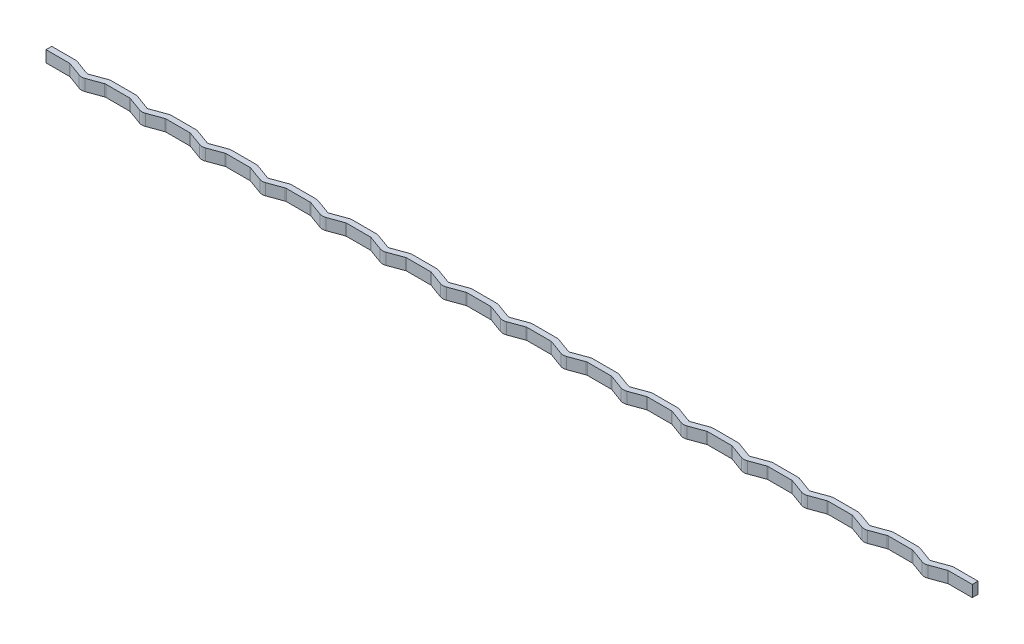
SolidWorks part; units mm, degrees
material "Rubber"
ref_plane "Front Plane" through (0, 0, 0) normal (0, 0, 1) x (1, 0, 0)
ref_plane "Top Plane" through (0, 0, 0) normal (0, 1, 0) x (1, 0, 0)
ref_plane "Right Plane" through (0, 0, 0) normal (1, 0, 0) x (0, 0, -1)
sketch "Sketch1" plane through (0, 0, 0) normal (0, 1, 0) x (1, 0, 0)
  line L0 (0, 0) -> (4.0737, 0)
  line L1 (4.25, 0) -> (10.25, 0) construction
  line L2 (7.25, 0.5445) -> (7.25, -3.0811) construction
  line L3 (10.4263, 0) -> (10.75, 0)
  line L4 (4.4157, -0.0603) -> (6.908, -0.9674)
  line L5 (7.592, -0.9674) -> (10.0843, -0.0603)
  line L6 (0, -0.5) -> (4.0737, -0.5)
  line L7 (4.2447, -0.5302) -> (6.737, -1.4373)
  line L8 (7.763, -1.4373) -> (10.2553, -0.5302)
  line L9 (10.4263, -0.5) -> (10.75, -0.5)
  line L10 (0, 0.5) -> (4.0737, 0.5)
  line L11 (4.5867, 0.4095) -> (7.079, -0.4976)
  line L12 (7.421, -0.4976) -> (9.9133, 0.4095)
  line L13 (10.4263, 0.5) -> (10.75, 0.5)
  line L14 (0, 0.5) -> (0, -0.5)
  line L15 (10.75, 0.5) -> (10.75, -0.5)
  arc A0 (4.4157, -0.0603) -> (4.0737, 0) centre (4.0737, -1) ccw
  arc A1 (10.4263, 0) -> (10.0843, -0.0603) centre (10.4263, -1) ccw
  arc A2 (7.592, -0.9674) -> (6.908, -0.9674) centre (7.25, -0.0277) cw
  arc A3 (4.2447, -0.5302) -> (4.0737, -0.5) centre (4.0737, -1) ccw
  arc A4 (7.763, -1.4373) -> (6.737, -1.4373) centre (7.25, -0.0277) cw
  arc A5 (10.4263, -0.5) -> (10.2553, -0.5302) centre (10.4263, -1) ccw
  arc A6 (4.5867, 0.4095) -> (4.0737, 0.5) centre (4.0737, -1) ccw
  arc A7 (7.421, -0.4976) -> (7.079, -0.4976) centre (7.25, -0.0277) cw
  arc A8 (10.4263, 0.5) -> (9.9133, 0.4095) centre (10.4263, -1) ccw
  point P17 (7.25, -1.0919)
  dimension "D5" = 1
  dimension "D6" = 1
  dimension "D7" = 1
  dimension "D1" = 4.25
  dimension "D2" = 6
  dimension "D3" = 0.5
  dimension "D4" = 160
  dimension "Section Length" = 10.75
  dimension "D10" = 4.0737
  dimension "D8" = 0.5
  dimension "D9" = 0.5
extrude "Boss-Extrude1" add sketch "Sketch1" along normal blind 2 contours L10 A6 L11 A7 L12 A8 L13 L15 L9 A5 L8 A4 L7 A3 L6 L14
pattern_linear "LPattern1" count 15 spacing 10.5 along (1, 0, 0) of "Boss-Extrude1"
sketch "Sketch2" plane through (0, 0, 0) normal (-1, 0, 0) x (0, 0, 1)
  line L1 (-0.5, 2) -> (0.5, 2)
  line L2 (-0.5, 2) -> (-0.5, 0)
  line L3 (-0.5, 0) -> (0.5, 0)
  line L4 (0.5, 2) -> (0.5, 0)
extrude "Boss-Extrude2" add sketch "Sketch2" against normal blind 4.0737 from offset 157.5
equation "\"OuterThickness\"= 3mm"
equation "\"MasterFillet\"= 3mm"
equation "\"PartSeperation\"= 6mm"
equation "\"D1@Sketch1\" = \"DiscThickness\" + \"LigamentExtension\" / 4"
equation "\"D2@Sketch1\"=\"PartSeperation\""
equation "\"D3@Sketch1\"=\"LigamentExtension\"/2"
equation "\"D4@Sketch1\" = 180 - \"LigamentAngle\""
equation "\"D7@Sketch1\"=\"MasterFillet\"/3"
equation "\"D6@Sketch1\"=\"MasterFillet\"/3"
equation "\"D5@Sketch1\"=\"MasterFillet\"/3"
equation "\"D9@Sketch1\" = \"LigamentDepth\" / 2"
equation "\"D8@Sketch1\" = \"LigamentDepth\" / 2"
equation "\"D1@Boss-Extrude1\" = \"LigamentThickness\""
equation "\"D3@LPattern1\"= \"DiscThickness\" + \"LigamentExtension\" / 2 + \"PartSeperation\""
equation "\"Tolerance\"= 0.15mm"
equation "\"HeightPart\"= 100mm"
equation "\"Holes\"= 1.5mm"
equation "\"SpineHolderThickness\"= 3mm"
equation "\"SpineHolderDepth\" = 3mm"
equation "\"LigamentExtension\"= 1mm"
equation "\"MotorLength\" = 40.5mm"
equation "\"MotorWidth\" = 20.3mm"
equation "\"AttachmentHeight\"= 3mm"
equation "\"SpoolDiameter\"= 60mm"
equation "\"SpoolHeight\"= 2mm"
equation "\"SpoolRidgeHeight\"= 1mm"
equation "\"SpoolRidgeDepth\"= 2mm"
equation "\"SpoolSeperation\"= 2mm"
equation "\"ServoHolderWidthOffset\"= 20mm"
equation "\"MotorTransmitterToScrew\"= 21.7mm"
equation "\"SpoolToSpine\"= 15mm"
equation "\"SpoolCenterToMotor\" = 31.5mm"
equation "\"HubOffset\"= 18mm"
equation "\"ServoFastenerHolders\"=2mm"
equation "\"ArduinoLength\" = 53.4mm"
equation "\"ArduinoWidth\" = 50mm"
equation "\"ArdYOffset\" = 29.5mm"
equation "\"ArdXOffset\" = 20.5mm"
equation "\"ArdXOffsetSmall\" = 25mm"
equation "\"MiddleServoOffset\"= 12mm"
equation "\"LargeServoOffset\"= 3mm"
equation "\"SmallServoOffset\"= 0mm"
equation "\"ToolHoleDiameter\"= 12mm"
equation "\"DiscThickness\"= 4mm"
equation "\"LigamentThickness\"= 2mm"
equation "\"LigamentAngle\"= 20deg"
equation "\"SpineDiameter\"= 15mm"
equation "\"LigamentDepth\"= 1mm"
equation "\"NoOfSegments\"= 3"
equation "\"DisksInSegments\"= 5"
equation "\"D1@LPattern1\"=\"NoOfSegments\"*\"DisksInSegments\""
equation "\"D19@Boss-Extrude2\"=(\"DiscThickness\" + \"LigamentExtension\" / 2 + \"PartSeperation\")*\"NoOfSegments\"*\"DisksInSegments\""
equation "\"D1@Boss-Extrude2\"=\"D10@Sketch1\""
equation "\"TendonExtension\" = 1mm"
